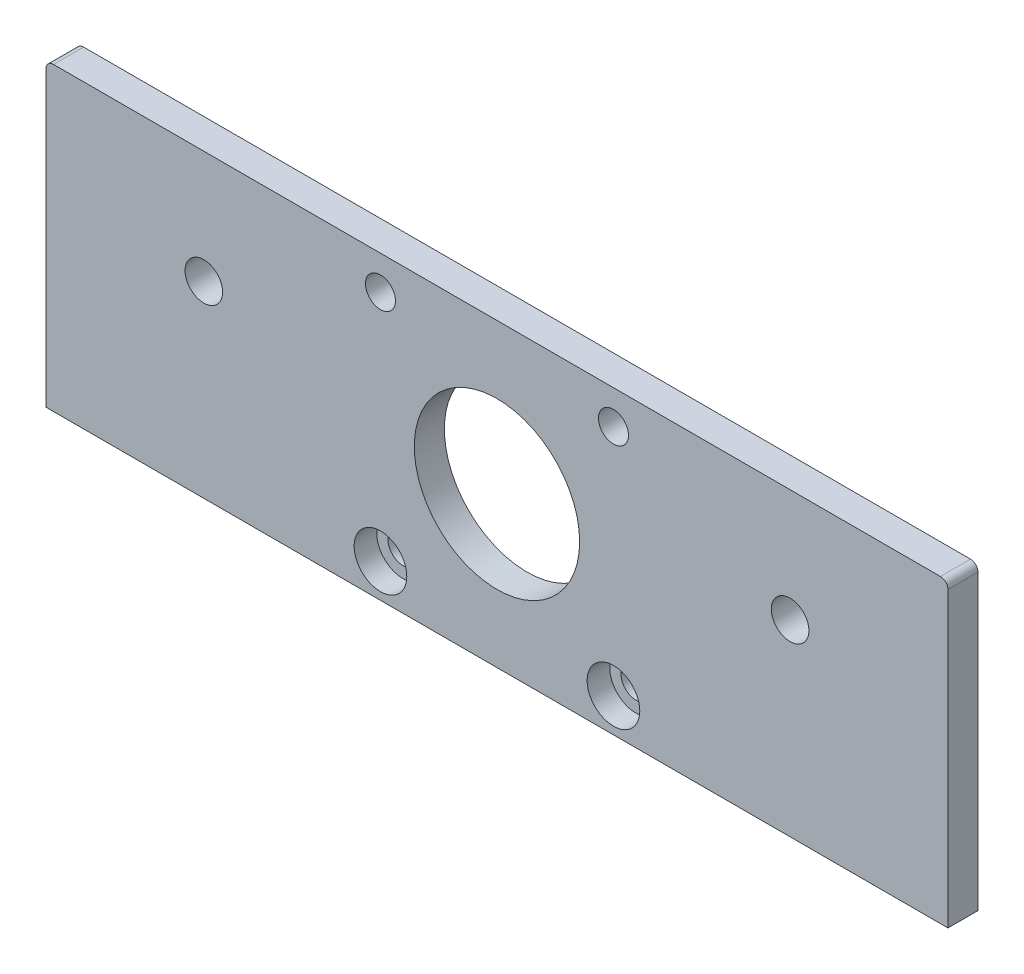
SolidWorks part; units mm, degrees
ref_plane "Front Plane" through (0, 0, 0) normal (0, 0, 1) x (1, 0, 0)
ref_plane "Top Plane" through (0, 0, 0) normal (0, 1, 0) x (1, 0, 0)
ref_plane "Right Plane" through (0, 0, 0) normal (1, 0, 0) x (0, 0, -1)
sketch "Sketch1" plane through (0, 0, 0) normal (0, 0, 1) x (1, 0, 0)
  line L1 (0, 0) -> (120, 0)
  line L2 (0, 0) -> (0, 40)
  line L3 (0, 40) -> (120, 40)
  line L4 (120, 0) -> (120, 40)
  circle A0 centre (21, 25) radius 2.5
  circle A1 centre (99, 25) radius 2.5
  circle A2 centre (60, 20) radius 11
  circle A3 centre (75.5, 35.5) radius 2
  circle A4 centre (75.5, 4.5) radius 2
  circle A5 centre (44.5, 4.5) radius 2
  circle A6 centre (44.5, 35.5) radius 2
extrude "Boss-Extrude1" add sketch "Sketch1" along normal blind 4
fillet "Fillet1" radius 1 2 edges at (120, 40, 2) (0, 40, 2)
sketch "Sketch2" plane through (0, 0, 4) normal (0, 0, 1) x (1, 0, 0)
  circle A0 centre (44.5, 4.5) radius 3.5
  circle A1 centre (75.5, 4.5) radius 3.5
extrude "Cut-Extrude1" cut sketch "Sketch2" against normal blind 3
